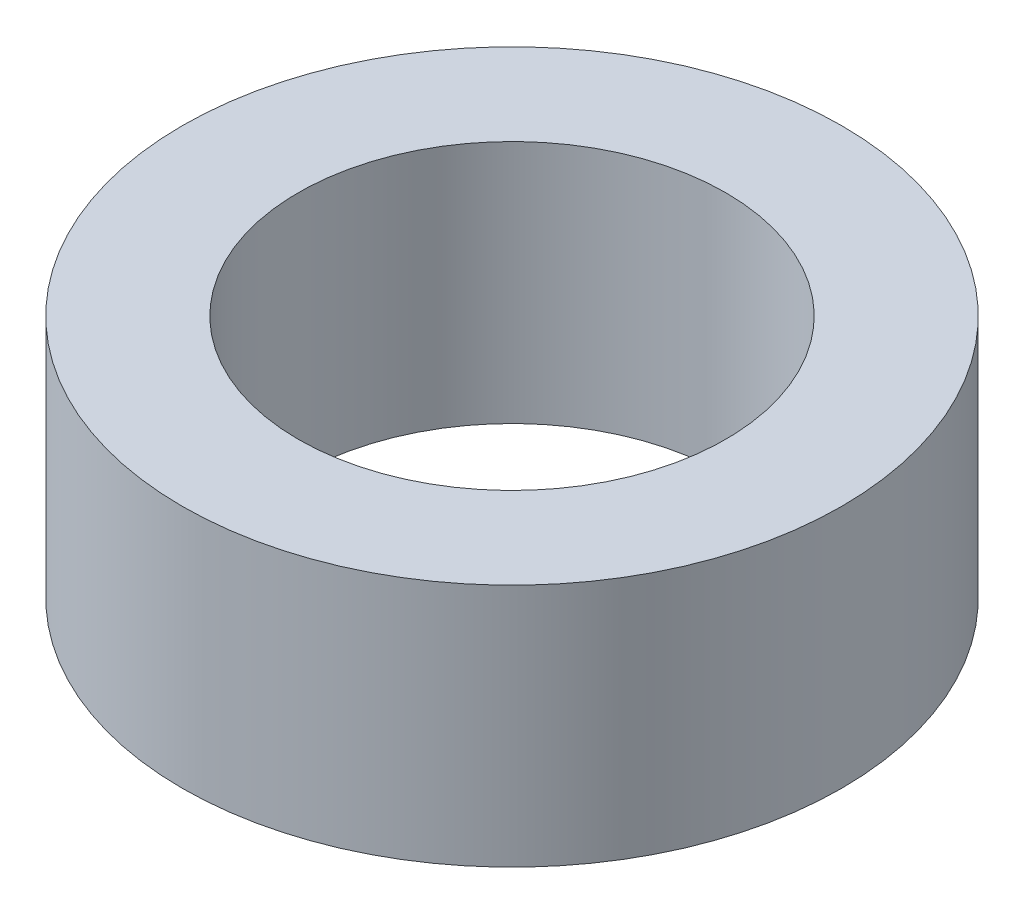
SolidWorks part; units mm, degrees
material "PTFE (general)"
ref_plane "Front Plane" through (0, 0, 0) normal (0, 0, 1) x (1, 0, 0)
ref_plane "Top Plane" through (0, 0, 0) normal (0, 1, 0) x (1, 0, 0)
ref_plane "Right Plane" through (0, 0, 0) normal (1, 0, 0) x (0, 0, -1)
sketch "Sketch1" plane through (0, 0, 0) normal (0, 1, 0) x (1, 0, 0)
  circle A0 centre (0, 0) radius 3.5
  circle A1 centre (0, 0) radius 5.4
extrude "Boss-Extrude1" add sketch "Sketch1" along normal blind 4
